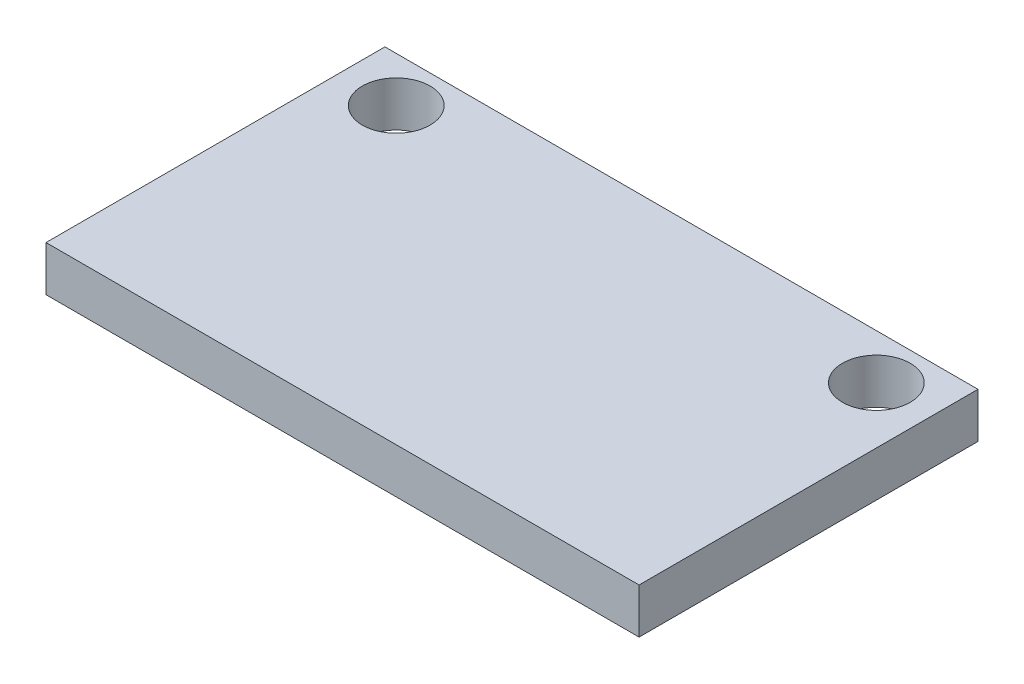
SolidWorks part; units mm, degrees
ref_plane "Front Plane" through (0, 0, 0) normal (0, 0, 1) x (1, 0, 0)
ref_plane "Top Plane" through (0, 0, 0) normal (0, 1, 0) x (1, 0, 0)
ref_plane "Right Plane" through (0, 0, 0) normal (1, 0, 0) x (0, 0, -1)
sketch "Sketch1" plane through (0, 0, 0) normal (0, 1, 0) x (1, 0, 0)
  line L0 (-13.125, 5.5) -> (-10.625, 5.5) construction
  line L1 (-13.125, 7.5) -> (13.125, 7.5)
  line L2 (-13.125, 7.5) -> (-13.125, -7.5)
  line L3 (-13.125, -7.5) -> (13.125, -7.5)
  line L4 (13.125, 7.5) -> (13.125, -7.5)
  line L5 (-13.125, 7.5) -> (13.125, -7.5) construction
  line L6 (-13.125, -7.5) -> (13.125, 7.5) construction
  line L8 (10.625, 5.5) -> (13.125, 5.5) construction
  circle A0 centre (-10.625, 5.5) radius 1.5
  circle A1 centre (10.625, 5.5) radius 1.5
  point P0 (0, 0)
  dimension "D5" = 3
  dimension "D1" = 15
  dimension "D2" = 26.25
  dimension "D3" = 2.5
  dimension "D4" = 2
extrude "Boss-Extrude1" add sketch "Sketch1" along normal mid plane 2
